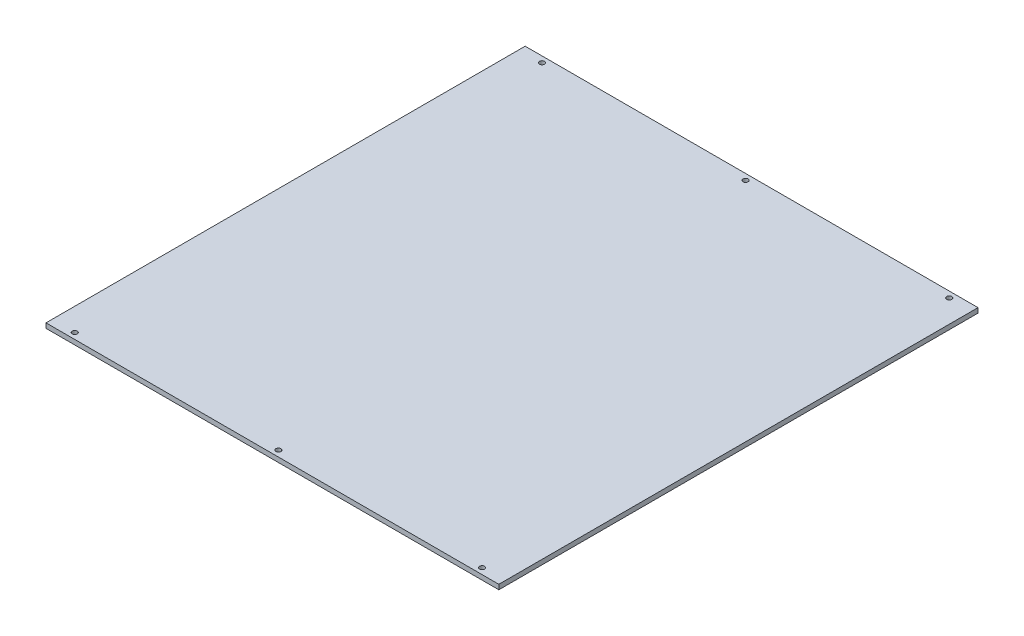
SolidWorks part; units mm, degrees
ref_plane "前视基准面" through (0, 0, 0) normal (0, 0, 1) x (1, 0, 0)
ref_plane "上视基准面" through (0, 0, 0) normal (0, 1, 0) x (1, 0, 0)
ref_plane "右视基准面" through (0, 0, 0) normal (1, 0, 0) x (0, 0, -1)
other "Configuration Table"
sketch "草图1" plane through (0, 0, 0) normal (0, 1, 0) x (1, 0, 0)
  line L1 (-513.8298, 189.4401) -> (-324.8298, 189.4401)
  line L2 (-513.8298, 189.4401) -> (-513.8298, -10.5599)
  line L3 (-513.8298, -10.5599) -> (-324.8298, -10.5599)
  line L4 (-324.8298, 189.4401) -> (-324.8298, -10.5599)
  dimension "D1" = 189
  dimension "D2" = 200
extrude "凸台-拉伸1" add sketch "草图1" along normal blind 2
sketch "草图2" plane through (0, 2, 0) normal (0, 1, 0) x (1, 0, 0)
  line L0 (-513.8298, 189.4401) -> (-513.8298, -10.5599) construction
  line L1 (-513.8298, -10.5599) -> (-324.8298, -10.5599) construction
  circle A0 centre (-504.3298, -8.0599) radius 1.05
  dimension "D1" = 9.5
  dimension "D2" = 2.5
extrude "切除-拉伸1" cut sketch "草图2" against normal blind 10
pattern_linear "阵列(线性)1" count 2 spacing 195 along (0, 0, -1) count 3 spacing 85 along (1, 0, 0) of "切除-拉伸1"
